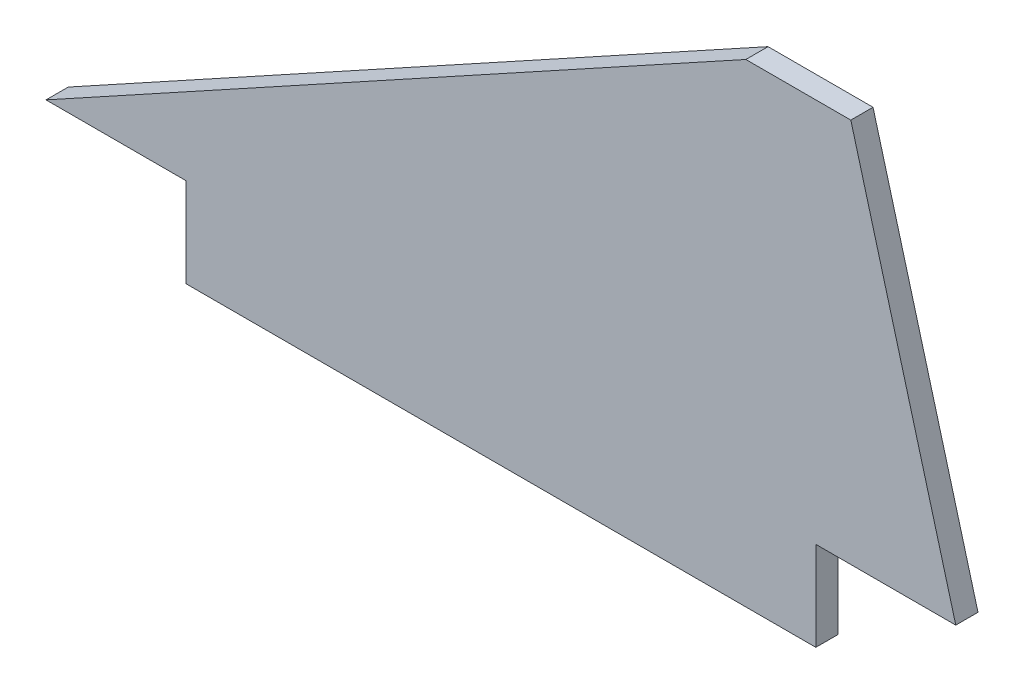
SolidWorks part; units mm, degrees
ref_plane "Front Plane" through (0, 0, 0) normal (0, 0, 1) x (1, 0, 0)
ref_plane "Top Plane" through (0, 0, 0) normal (0, 1, 0) x (1, 0, 0)
ref_plane "Right Plane" through (0, 0, 0) normal (1, 0, 0) x (0, 0, -1)
sketch "Sketch1" plane through (0, 0, 0) normal (0, 0, 1) x (1, 0, 0)
  line L0 (0, 0) -> (20, 0)
  line L1 (20, 0) -> (20, -12.75)
  line L2 (20, -12.75) -> (110, -12.75)
  line L3 (110, -12.75) -> (110, 0)
  line L4 (110, 0) -> (130, 0)
  line L5 (130, 0) -> (115, 55)
  line L6 (115, 55) -> (100, 55)
  line L7 (100, 55) -> (0, 0)
  dimension "D1" = 20
  dimension "D2" = 12.75
  dimension "D3" = 90
  dimension "D4" = 20
  dimension "D5" = 15
  dimension "D6" = 15
  dimension "D7" = 55
extrude "Boss-Extrude1" add sketch "Sketch1" along normal blind 3.175
